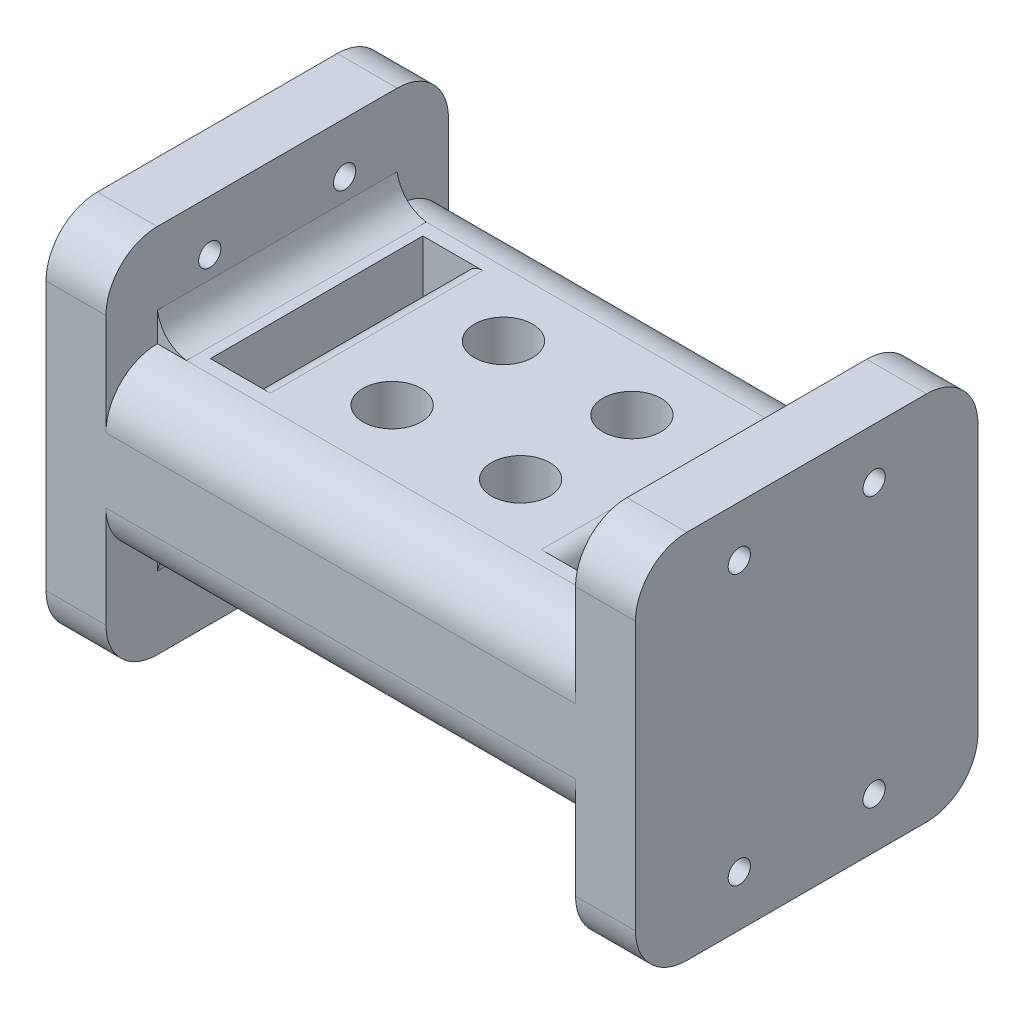
SolidWorks part; units mm, degrees
ref_plane "Front Plane" through (0, 0, 0) normal (0, 0, 1) x (1, 0, 0)
ref_plane "Top Plane" through (0, 0, 0) normal (0, 1, 0) x (1, 0, 0)
ref_plane "Right Plane" through (0, 0, 0) normal (1, 0, 0) x (0, 0, -1)
sketch "Sketch1" plane through (0, 0, 0) normal (1, 0, 0) x (0, 0, -1)
  line L0 (10, 20) -> (-10, 20) construction
  line L1 (-25.4, 27.5) -> (25.4, 27.5)
  line L2 (-25.4, 27.5) -> (-25.4, -27.5)
  line L3 (-25.4, -27.5) -> (25.4, -27.5)
  line L4 (25.4, 27.5) -> (25.4, -27.5)
  line L5 (-10, -20) -> (10, -20) construction
  line L6 (0, 20) -> (0, -20) construction
  circle A0 centre (-10, 20) radius 1.651
  circle A1 centre (10, 20) radius 1.651
  circle A2 centre (-10, -20) radius 1.651
  circle A3 centre (10, -20) radius 1.651
  point P4 (0, 27.5)
  point P6 (25.4, 0)
  point P17 (0, 0)
  dimension "D7" = 3.302
  dimension "D1" = 50.8
  dimension "D2" = 55
  dimension "D3" = 40
  dimension "D4" = 20
extrude "Boss-Extrude1" add sketch "Sketch1" along normal blind 8.89
fillet "Fillet1" radius 7.62 4 edges at (4.445, 27.5, -25.4) (4.445, -27.5, -25.4) (4.445, -27.5, 25.4) (4.445, 27.5, 25.4)
sketch "Sketch2" plane through (8.89, 0, 0) normal (1, 0, 0) x (0, 0, -1)
  line L0 (-25.4, 19.88) -> (-25.4, -19.88) construction
  line L1 (-25.4, 12.446) -> (25.4, 12.446)
  line L2 (-25.4, 12.446) -> (-25.4, -12.446)
  line L3 (-25.4, -12.446) -> (25.4, -12.446)
  line L4 (25.4, 12.446) -> (25.4, -12.446)
  line L5 (25.4, -19.88) -> (25.4, 19.88) construction
  point P8 (25.4, 0)
  dimension "D1" = 24.892
extrude "Boss-Extrude2" add sketch "Sketch2" along normal blind 34.8196
fillet "Fillet2" radius 7.62 4 edges at (26.2998, -12.446, -25.4) (26.2998, 12.446, -25.4) (26.2998, -12.446, 25.4) (26.2998, 12.446, 25.4)
mirror "Mirror6" about plane through (43.7096, 0, 0) normal (1, 0, 0) of bodies 105
sketch "Sketch7" plane through (0, 12.446, 0) normal (0, 1, 0) x (1, 0, 0)
  circle A0 centre (34.1846, 8.255) radius 4.318
  circle A1 centre (34.1846, -8.255) radius 4.318
  circle A2 centre (53.2346, 8.255) radius 4.318
  circle A3 centre (53.2346, -8.255) radius 4.318
  point P12 (0, 0)
  point P13 (0, 0)
  point P14 (0, 0)
  point P15 (0, 0)
  dimension "D1" = 16.51
  dimension "D3" = 8.636
  dimension "D4" = 8.636
  dimension "D5" = 8.636
  dimension "D6" = 8.636
  dimension "D2" = 19.05
  dimension "D7" = 16.51
  dimension "D8" = 19.05
extrude "Cut-Extrude4" cut sketch "Sketch7" against normal through all
sketch "Sketch8" plane through (87.4192, 0, 0) normal (1, 0, 0) x (0, 0, -1)
  circle A0 centre (-10, 20) radius 3.556
  circle A1 centre (-10, -20) radius 3.556
  circle A2 centre (10, 20) radius 3.556
  circle A3 centre (10, -20) radius 3.556
sketch "Sketch9" plane through (0, 0, 25.4) normal (0, 0, 1) x (1, 0, 0)
  line L0 (8.89, 16.764) -> (8.89, 12.446)
  line L1 (8.89, 19.88) -> (8.89, 4.826) construction
  line L2 (8.89, 12.446) -> (13.208, 12.446)
  line L3 (8.89, 12.446) -> (78.5292, 12.446) construction
  line L4 (8.89, 16.764) -> (13.208, 12.446)
  line L5 (8.89, 12.446) -> (10.3268, 13.8828)
  spline S0 degree 2 poles (8.89, 16.764) (9.6047, 13.1607) (13.208, 12.446) knots 0 0 0 1 1 1
  line M13 (8.89, 4.826) -> (8.89, 19.88)
extrude "Boss-Extrude4" add sketch "Sketch9" against normal up to vertex (43.18 mm away) from vertex at -7.62 contours S0 L5 L2 | S0 L5 M13
mirror "Mirror8" about plane through (0, 0, 0) normal (0, 1, 0) of "Boss-Extrude4"
ref_plane "Plane1" through (43.7096, 0, 0) normal (1, 0, 0) x (0, 0, -1)
mirror "Mirror9" about plane through (43.7096, 0, 0) normal (1, 0, 0) of "Mirror8", "Boss-Extrude4"
sketch "Sketch10" plane through (0, 12.446, 0) normal (0, 1, 0) x (1, 0, 0)
  line L0 (14.732, 15.748) -> (14.732, -15.748)
  line L1 (14.732, -15.748) -> (21.082, -15.748)
  line L2 (21.082, -15.748) -> (21.082, 15.748)
  line L3 (21.082, 15.748) -> (14.732, 15.748)
  line L4 (8.89, 17.78) -> (8.89, -17.78) construction
  line L5 (13.208, -17.78) -> (74.2112, -17.78) construction
  line L6 (74.2112, 17.78) -> (13.208, 17.78) construction
  point P15 (15.887, 10.019)
  point P16 (14.732, 10.5673)
  point P17 (15.2963, 12.9488)
  point P26 (16.2459, 15.748)
  point P27 (15.2345, 13.2555)
  dimension "D1" = 5.842
  dimension "D2" = 6.35
  dimension "D3" = 31.496
  dimension "D4" = 2.032
  dimension "D5" = 2.032
extrude "Cut-Extrude5" cut sketch "Sketch10" against normal through all
mirror "Mirror10" about plane through (43.7096, 0, 0) normal (1, 0, 0) of "Cut-Extrude5"
fillet "Fillet4" radius 2.54 4 edges at (21.082, -12.446, 0) (66.3372, -12.446, 0) (66.3372, 12.446, 0) (21.082, 12.446, 0)
